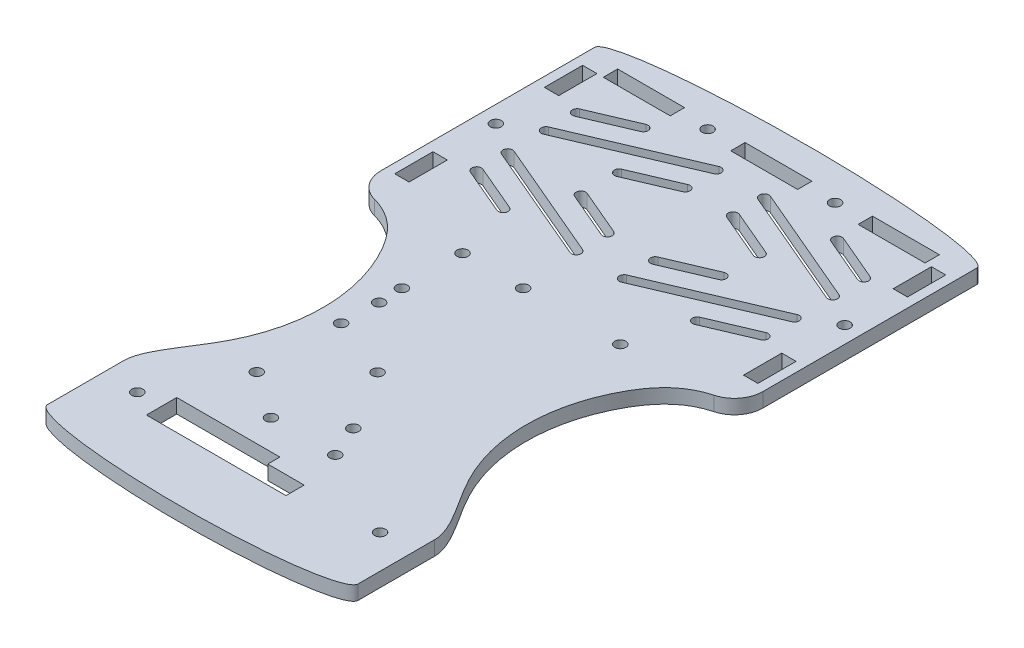
SolidWorks part; units mm, degrees
ref_plane "Front Plane" through (0, 0, 0) normal (0, 0, 1) x (1, 0, 0)
ref_plane "Top Plane" through (0, 0, 0) normal (0, 1, 0) x (1, 0, 0)
ref_plane "Right Plane" through (0, 0, 0) normal (1, 0, 0) x (0, 0, -1)
sketch "Sketch1" plane through (0, 0, 0) normal (0, 1, 0) x (1, 0, 0)
  line L1 (40, 50) -> (-40, 50)
  line L2 (40, 50) -> (40, -50)
  line L3 (40, -50) -> (-40, -50)
  line L4 (-40, 50) -> (-40, -50)
  line L5 (40, 50) -> (-40, -50) construction
  line L6 (40, -50) -> (-40, 50) construction
  point P0 (0, 0)
  dimension "D1" = 80
  dimension "D2" = 100
extrude "Boss-Extrude1" add sketch "Sketch1" along normal mid plane 3
sketch "Sketch2" plane through (0, 1.5, 0) normal (0, 1, 0) x (1, 0, 0)
  line L0 (0, 50) -> (0, 32.5) construction
  line L1 (40, 50) -> (-40, 50) construction
  line L2 (-7, 47) -> (-13.3333, 47) construction
  line L3 (-40, 50) -> (-40, -50) construction
  line L4 (-13.3333, 47) -> (-19.6667, 47) construction
  line L5 (-13.3333, 47) -> (-13.3333, 48.15) construction
  line L6 (-33.6667, 48.5) -> (-19.6667, 48.5)
  line L7 (-33.6667, 48.5) -> (-33.6667, 45.5)
  line L8 (-33.6667, 45.5) -> (-19.6667, 45.5)
  line L9 (-19.6667, 48.5) -> (-19.6667, 45.5)
  line L10 (-13.3333, 48.15) -> (-19.6667, 48.15) construction
  line L11 (-33.6667, 48.15) -> (-40, 48.15) construction
  line L12 (0, 47) -> (7, 48.5) construction
  line L13 (7, 48.5) -> (-7, 48.5)
  line L14 (0, 47) -> (7, 45.5) construction
  line L15 (7, 45.5) -> (-7, 45.5)
  line L16 (-7, 48.5) -> (-7, 45.5)
  line L17 (0, 47) -> (-7, 45.5) construction
  line L18 (0, 47) -> (-7, 48.5) construction
  line L19 (13.3333, 48.15) -> (19.6667, 48.15) construction
  line L20 (13.3333, 47) -> (13.3333, 48.15) construction
  line L21 (13.3333, 47) -> (19.6667, 47) construction
  line L22 (7, 47) -> (13.3333, 47) construction
  line L23 (7, 48.5) -> (7, 45.5)
  line L24 (19.6667, 48.5) -> (19.6667, 45.5)
  line L25 (33.6667, 45.5) -> (19.6667, 45.5)
  line L26 (33.6667, 48.5) -> (33.6667, 45.5)
  line L27 (33.6667, 48.5) -> (19.6667, 48.5)
  circle A0 centre (-13.3333, 47) radius 1.15
  circle A1 centre (13.3333, 47) radius 1.15
  point P25 (0, 48.5)
  point P34 (0, 45.5)
  dimension "D1" = 2.3
  dimension "D2" = 3
  dimension "D3" = 3
  dimension "D4" = 3
  dimension "D5" = 14
  dimension "D6" = 7
extrude "Cut-Extrude1" cut sketch "Sketch2" against normal through all
sketch "Sketch3" plane through (0, 1.5, 0) normal (0, 1, 0) x (1, 0, 0)
  line L0 (36.5, 24.6918) -> (36.5, 26.9918) construction
  line L1 (-35, 45.5) -> (-38, 45.5)
  line L2 (-35, 45.5) -> (-35, 37.5)
  line L3 (-35, 37.5) -> (-38, 37.5)
  line L4 (-38, 45.5) -> (-38, 37.5)
  line L5 (-35, 14.1836) -> (-38, 14.1836)
  line L6 (-35, 14.1836) -> (-35, 6.1836)
  line L7 (-35, 6.1836) -> (-38, 6.1836)
  line L8 (-38, 14.1836) -> (-38, 6.1836)
  line L9 (38, 14.1836) -> (35, 14.1836)
  line L10 (38, 14.1836) -> (38, 6.1836)
  line L11 (38, 6.1836) -> (35, 6.1836)
  line L12 (35, 14.1836) -> (35, 6.1836)
  line L13 (35, 37.5) -> (38, 37.5)
  line L14 (35, 37.5) -> (35, 45.5)
  line L15 (35, 45.5) -> (38, 45.5)
  line L16 (38, 37.5) -> (38, 45.5)
  line L17 (38, 24.6918) -> (35, 24.6918) construction
  line L18 (38, 26.9918) -> (35, 26.9918) construction
  line L19 (-36.5, 26.9918) -> (-36.5, 24.6918) construction
  line L20 (-35, 26.9918) -> (-38, 26.9918) construction
  line L21 (-35, 24.6918) -> (-38, 24.6918) construction
  circle A0 centre (36.5, 25.8418) radius 1.15
  circle A1 centre (-36.5, 25.8418) radius 1.15
  dimension "D1" = 2.3
  dimension "D2" = 2.3
extrude "Cut-Extrude2" cut sketch "Sketch3" against normal through all
sketch "Sketch4" plane through (0, 1.5, 0) normal (0, 1, 0) x (1, 0, 0)
  line L0 (0, 25.8418) -> (35, 25.8418) construction
  line L1 (35, 6.1836) -> (-35, 6.1836) construction
  line L2 (35, 6.1836) -> (35, 45.5) construction
  line L3 (35, 45.5) -> (-35, 45.5) construction
  line L4 (-35, 6.1836) -> (-35, 45.5) construction
  line L5 (30, 29.8418) -> (5, 40.5) construction
  line L6 (29.6078, 28.9219) -> (4.6078, 39.5801)
  line L7 (0, 45.5) -> (0, 6.1836) construction
  line L8 (30.3922, 30.7617) -> (5.3922, 41.4199)
  line L9 (14.7007, 29.8418) -> (5, 33.9775) construction
  line L10 (14.3085, 28.9219) -> (4.6078, 33.0576)
  line L11 (15.0929, 30.7617) -> (5.3922, 34.8974)
  line L12 (5, 40.5) -> (5, 33.9775) construction
  line L13 (30, 29.8418) -> (14.7007, 29.8418) construction
  line L17 (5, 33.9775) -> (5, 27.455) construction
  line L18 (-0.5986, 29.8418) -> (14.7007, 29.8418) construction
  line L19 (20.2993, 40.5) -> (30, 36.3643) construction
  line L20 (20.6915, 41.4199) -> (30.3922, 37.2842)
  line L21 (19.9071, 39.5801) -> (29.6078, 35.4444)
  line L22 (30, 36.3643) -> (30, 29.8418) construction
  line L23 (20.2993, 40.5) -> (5, 40.5) construction
  line L27 (35.5986, 40.5) -> (20.2993, 40.5) construction
  line L28 (30, 36.3643) -> (30, 42.8868) construction
  line L29 (30, 40.5) -> (30, 42.8868) construction
  line L30 (35.5986, 40.5) -> (30, 40.5) construction
  line L31 (-0.5986, 29.8418) -> (5, 29.8418) construction
  line L32 (5, 29.8418) -> (5, 27.455) construction
  line L33 (30, 21.8418) -> (5, 11.1836) construction
  line L34 (29.6078, 22.7617) -> (4.6078, 12.1035)
  line L35 (30.3922, 20.9219) -> (5.3922, 10.2637)
  line L36 (14.7007, 21.8418) -> (5, 17.7061) construction
  line L37 (14.3085, 22.7617) -> (4.6078, 18.626)
  line L38 (15.0929, 20.9219) -> (5.3922, 16.7862)
  line L42 (20.2993, 11.1836) -> (30, 15.3193) construction
  line L43 (20.6915, 10.2637) -> (30.3922, 14.3994)
  line L44 (19.9071, 12.1035) -> (29.6078, 16.2392)
  line L48 (5, 21.8418) -> (5, 24.2286) construction
  line L49 (-0.5986, 21.8418) -> (5, 21.8418) construction
  line L50 (35.5986, 11.1836) -> (30, 11.1836) construction
  line L51 (30, 11.1836) -> (30, 8.7968) construction
  line L52 (30, 15.3193) -> (30, 8.7968) construction
  line L53 (35.5986, 11.1836) -> (20.2993, 11.1836) construction
  line L54 (20.2993, 11.1836) -> (5, 11.1836) construction
  line L55 (30, 15.3193) -> (30, 21.8418) construction
  line L56 (-0.5986, 21.8418) -> (14.7007, 21.8418) construction
  line L57 (5, 17.7061) -> (5, 24.2286) construction
  line L58 (30, 21.8418) -> (14.7007, 21.8418) construction
  line L59 (5, 11.1836) -> (5, 17.7061) construction
  line L60 (-30, 29.8418) -> (-5, 40.5) construction
  line L61 (-29.6078, 28.9219) -> (-4.6078, 39.5801)
  line L62 (-30.3922, 30.7617) -> (-5.3922, 41.4199)
  line L63 (-14.7007, 29.8418) -> (-5, 33.9775) construction
  line L64 (-14.3085, 28.9219) -> (-4.6078, 33.0576)
  line L65 (-15.0929, 30.7617) -> (-5.3922, 34.8974)
  line L69 (-20.2993, 40.5) -> (-30, 36.3643) construction
  line L70 (-20.6915, 41.4199) -> (-30.3922, 37.2842)
  line L71 (-19.9071, 39.5801) -> (-29.6078, 35.4444)
  line L75 (-30, 21.8418) -> (-5, 11.1836) construction
  line L76 (-29.6078, 22.7617) -> (-4.6078, 12.1035)
  line L77 (-30.3922, 20.9219) -> (-5.3922, 10.2637)
  line L78 (-14.7007, 21.8418) -> (-5, 17.7061) construction
  line L79 (-14.3085, 22.7617) -> (-4.6078, 18.626)
  line L80 (-15.0929, 20.9219) -> (-5.3922, 16.7862)
  line L84 (-20.2993, 11.1836) -> (-30, 15.3193) construction
  line L85 (-20.6915, 10.2637) -> (-30.3922, 14.3994)
  line L86 (-19.9071, 12.1035) -> (-29.6078, 16.2392)
  line L90 (-5, 11.1836) -> (-5, 17.7061) construction
  line L91 (-30, 21.8418) -> (-14.7007, 21.8418) construction
  line L92 (-5, 17.7061) -> (-5, 24.2286) construction
  line L93 (0.5986, 21.8418) -> (-14.7007, 21.8418) construction
  line L94 (-30, 15.3193) -> (-30, 21.8418) construction
  line L95 (-20.2993, 11.1836) -> (-5, 11.1836) construction
  line L96 (-35.5986, 11.1836) -> (-20.2993, 11.1836) construction
  line L97 (-30, 15.3193) -> (-30, 8.7968) construction
  line L98 (-30, 11.1836) -> (-30, 8.7968) construction
  line L99 (-35.5986, 11.1836) -> (-30, 11.1836) construction
  line L100 (0.5986, 21.8418) -> (-5, 21.8418) construction
  line L101 (-5, 21.8418) -> (-5, 24.2286) construction
  line L102 (-5, 29.8418) -> (-5, 27.455) construction
  line L103 (0.5986, 29.8418) -> (-5, 29.8418) construction
  line L104 (-35.5986, 40.5) -> (-30, 40.5) construction
  line L105 (-30, 40.5) -> (-30, 42.8868) construction
  line L106 (-30, 36.3643) -> (-30, 42.8868) construction
  line L107 (-35.5986, 40.5) -> (-20.2993, 40.5) construction
  line L108 (-20.2993, 40.5) -> (-5, 40.5) construction
  line L109 (-30, 36.3643) -> (-30, 29.8418) construction
  line L110 (0.5986, 29.8418) -> (-14.7007, 29.8418) construction
  line L111 (-5, 33.9775) -> (-5, 27.455) construction
  line L112 (-30, 29.8418) -> (-14.7007, 29.8418) construction
  line L113 (-5, 40.5) -> (-5, 33.9775) construction
  arc A0 (29.6078, 28.9219) -> (30.3922, 30.7617) centre (30, 29.8418) ccw
  arc A1 (5.3922, 41.4199) -> (4.6078, 39.5801) centre (5, 40.5) ccw
  arc A2 (14.3085, 28.9219) -> (15.0929, 30.7617) centre (14.7007, 29.8418) ccw
  arc A3 (5.3922, 34.8974) -> (4.6078, 33.0576) centre (5, 33.9775) ccw
  arc A6 (20.6915, 41.4199) -> (19.9071, 39.5801) centre (20.2993, 40.5) ccw
  arc A7 (29.6078, 35.4444) -> (30.3922, 37.2842) centre (30, 36.3643) ccw
  arc A12 (29.6078, 22.7617) -> (30.3922, 20.9219) centre (30, 21.8418) cw
  arc A13 (5.3922, 10.2637) -> (4.6078, 12.1035) centre (5, 11.1836) cw
  arc A14 (14.3085, 22.7617) -> (15.0929, 20.9219) centre (14.7007, 21.8418) cw
  arc A15 (5.3922, 16.7862) -> (4.6078, 18.626) centre (5, 17.7061) cw
  arc A18 (20.6915, 10.2637) -> (19.9071, 12.1035) centre (20.2993, 11.1836) cw
  arc A19 (29.6078, 16.2392) -> (30.3922, 14.3994) centre (30, 15.3193) cw
  arc A24 (-29.6078, 28.9219) -> (-30.3922, 30.7617) centre (-30, 29.8418) cw
  arc A25 (-5.3922, 41.4199) -> (-4.6078, 39.5801) centre (-5, 40.5) cw
  arc A26 (-14.3085, 28.9219) -> (-15.0929, 30.7617) centre (-14.7007, 29.8418) cw
  arc A27 (-5.3922, 34.8974) -> (-4.6078, 33.0576) centre (-5, 33.9775) cw
  arc A30 (-20.6915, 41.4199) -> (-19.9071, 39.5801) centre (-20.2993, 40.5) cw
  arc A31 (-29.6078, 35.4444) -> (-30.3922, 37.2842) centre (-30, 36.3643) cw
  arc A34 (-29.6078, 22.7617) -> (-30.3922, 20.9219) centre (-30, 21.8418) ccw
  arc A35 (-5.3922, 10.2637) -> (-4.6078, 12.1035) centre (-5, 11.1836) ccw
  arc A36 (-14.3085, 22.7617) -> (-15.0929, 20.9219) centre (-14.7007, 21.8418) ccw
  arc A37 (-5.3922, 16.7862) -> (-4.6078, 18.626) centre (-5, 17.7061) ccw
  arc A40 (-20.6915, 10.2637) -> (-19.9071, 12.1035) centre (-20.2993, 11.1836) ccw
  arc A41 (-29.6078, 16.2392) -> (-30.3922, 14.3994) centre (-30, 15.3193) ccw
  point P10 (17.5, 35.1709)
  point P19 (9.8504, 31.9096)
  point P39 (25.1496, 38.4322)
  point P61 (17.5, 16.5127)
  point P68 (9.8504, 19.774)
  point P82 (25.1496, 13.2515)
  point P110 (-17.5, 35.1709)
  point P117 (-9.8504, 31.9096)
  point P131 (-25.1496, 38.4322)
  point P145 (-17.5, 16.5127)
  point P152 (-9.8504, 19.774)
  point P166 (-25.1496, 13.2515)
  dimension "D1" = 1
  dimension "D2" = 5
  dimension "D3" = 5
  dimension "D4" = 5
  dimension "D5" = 4
  dimension "D6" = 6
extrude "Cut-Extrude3" cut sketch "Sketch4" against normal through all
sketch "Sketch5" plane through (0, 1.5, 0) normal (0, 1, 0) x (1, 0, 0)
  line L0 (40, 50) -> (-40, 50) construction
  line L1 (40, 50) -> (-40, 50)
  ellipse E0 centre (0, 50) end of major axis (-40, 50) minor radius 4.5 (40, 50) -> (-40, 50) ccw
  dimension "D1" = 4.5
extrude "Boss-Extrude2" add sketch "Sketch5" against normal up to vertex (3 mm away)
sketch "Sketch6" plane through (0, -1.5, 0) normal (0, -1, 0) x (1, 0, 0)
  line L0 (0, 0) -> (0, 50) construction
  line L1 (-40, 50) -> (40, 50) construction
sketch "Sketch9" plane through (0, 1.5, 0) normal (0, 1, 0) x (1, 0, 0)
  line L0 (40, -50) -> (40, 50) construction
  line L1 (-40, -50) -> (40, -50)
  line L2 (-40, -50) -> (-40, -56)
  line L3 (-40, -56) -> (40, -56)
  line L4 (40, -50) -> (40, -56)
  dimension "D1" = 6
extrude "Boss-Extrude3" add sketch "Sketch9" against normal up to vertex (3 mm away)
sketch "Sketch7" plane through (0, 1.5, 0) normal (0, 1, 0) x (1, 0, 0)
  line L2 (40, 0) -> (67.1145, 0) construction
  line L3 (32.5, -56) -> (32.5, -57.6455) construction
  line L4 (40, 0) -> (40, -56)
  line L5 (40, -56) -> (32.5, -56)
  line L6 (0, 0) -> (0, -51.1929) construction
  line L7 (-32.5, -56) -> (-32.5, -57.6455) construction
  line L8 (-40, -56) -> (-32.5, -56)
  line L9 (-40, 0) -> (-40, -56)
  line L10 (40, -56) -> (40, 50) construction
  line L11 (-40, -56) -> (40, -56) construction
  spline S0 degree 3 poles (40, 0) (32.0981, 0) (20.5513, -12.4671) (19.3397, -36.9328) (32.5, -51.978) (32.5, -56) knots 0 0 0 0 0.26869 0.752948 1 1 1 1
  spline S1 degree 3 poles (-40, 0) (-32.0981, 0) (-20.5513, -12.4671) (-19.3397, -36.9328) (-32.5, -51.978) (-32.5, -56) knots 0 0 0 0 0.26869 0.752948 1 1 1 1
  dimension "D1" = 65
extrude "Cut-Extrude4" cut sketch "Sketch7" against normal through all
sketch "Sketch11" plane through (0, -1.5, 0) normal (0, -1, 0) x (1, 0, 0)
  line L0 (32.5, 56) -> (32.5, 72)
  line L1 (-32.5, 56) -> (-32.5, 72)
  line L2 (-32.5, 56) -> (32.5, 56)
  ellipse E0 centre (0, 72) end of major axis (32.5, 72) minor radius 4.5 (32.5, 72) -> (-32.5, 72) ccw
  point P7 (0, 56)
  dimension "D1" = 4.5
  dimension "D2" = 16
extrude "Boss-Extrude4" add sketch "Sketch11" against normal up to vertex (3 mm away)
sketch "Sketch12" plane through (0, 1.5, 0) normal (0, 1, 0) x (1, 0, 0)
  circle A0 centre (-6.731, -51) radius 1.143
  circle A1 centre (6.731, -51) radius 1.143
  circle A2 centre (6.731, -51) radius 1.143 construction
  circle A3 centre (-6.731, -51) radius 1.143 construction
extrude "Cut-Extrude5" cut sketch "Sketch12" against normal through all
sketch "Sketch13" plane through (0, 1.5, 0) normal (0, 1, 0) x (1, 0, 0)
  circle A0 centre (25.46, -60.3564) radius 1.15
  circle A1 centre (-25.34, -60.3564) radius 1.15
  dimension "D1" = 2.3
extrude "Cut-Extrude6" cut sketch "Sketch13" against normal through all
sketch "Sketch15" plane through (0, -1.5, 0) normal (0, -1, 0) x (1, 0, 0)
  line L0 (-18.355, 59.0864) -> (-18.355, 57.1814) construction
  line L1 (1.33, 57.1814) -> (-20.26, 57.1814)
  line L2 (8.95, 59.7214) -> (8.95, 63.5314)
  line L3 (8.95, 63.5314) -> (-20.26, 63.5314)
  line L4 (-20.26, 57.1814) -> (-20.26, 63.5314)
  line L5 (-18.355, 59.0864) -> (-20.26, 59.0864) construction
  line L6 (7.045, 61.6264) -> (7.045, 63.5314) construction
  line L7 (7.045, 61.6264) -> (8.95, 61.6264) construction
  line L8 (8.95, 59.7214) -> (1.33, 59.7214)
  line L9 (1.33, 59.7214) -> (1.33, 57.1814)
  line L10 (7.045, 61.6264) -> (7.045, 59.7214) construction
  line L11 (-0.575, 59.0864) -> (1.33, 59.0864) construction
  line L12 (-0.575, 59.0864) -> (-0.575, 57.1814) construction
  dimension "D1" = 1.905
extrude "Cut-Extrude7" cut sketch "Sketch15" against normal through all
fillet "Fillet1" radius 6 2 edges at (40, 0, 0) (-40, 0, 0)
sketch "Sketch16" plane through (0, -1.5, 0) normal (0, -1, 0) x (1, 0, 0)
  line L0 (-3.81, 1.1264) -> (-3.81, 44.195) construction
  line L1 (-3.81, 44.195) -> (-16.4994, 44.195) construction
  line L2 (-3.81, 22.6607) -> (-12.7886, 22.6607) construction
  line L3 (-3.81, 1.1264) -> (-16.2968, 1.1264) construction
  line L4 (-16.2968, 1.1264) -> (-16.2968, 18.7958) construction
  circle A0 centre (-16.4994, 44.195) radius 1.15
  circle A1 centre (-16.51, 13.8264) radius 1.15
  circle A2 centre (16.51, 1.1264) radius 1.15
  circle A3 centre (3.81, 44.3064) radius 1.15
  circle A4 centre (-3.81, 1.1264) radius 1.15
  circle A5 centre (-16.2968, 18.7958) radius 1.15
  circle A6 centre (-16.51, 1.1264) radius 1.15
  circle A7 centre (-16.51, 26.5264) radius 1.15
  circle A8 centre (-3.81, 31.6064) radius 1.15
  circle A9 centre (-16.51, 44.3064) radius 1.15
  dimension "D1" = 2.3
  dimension "D2" = 2.3
  dimension "D3" = 2.3
extrude "Cut-Extrude8" cut sketch "Sketch16" against normal through all contours A1 | A5 | A7 | A3 | A4 | A2 | A6 | A8 | A0
